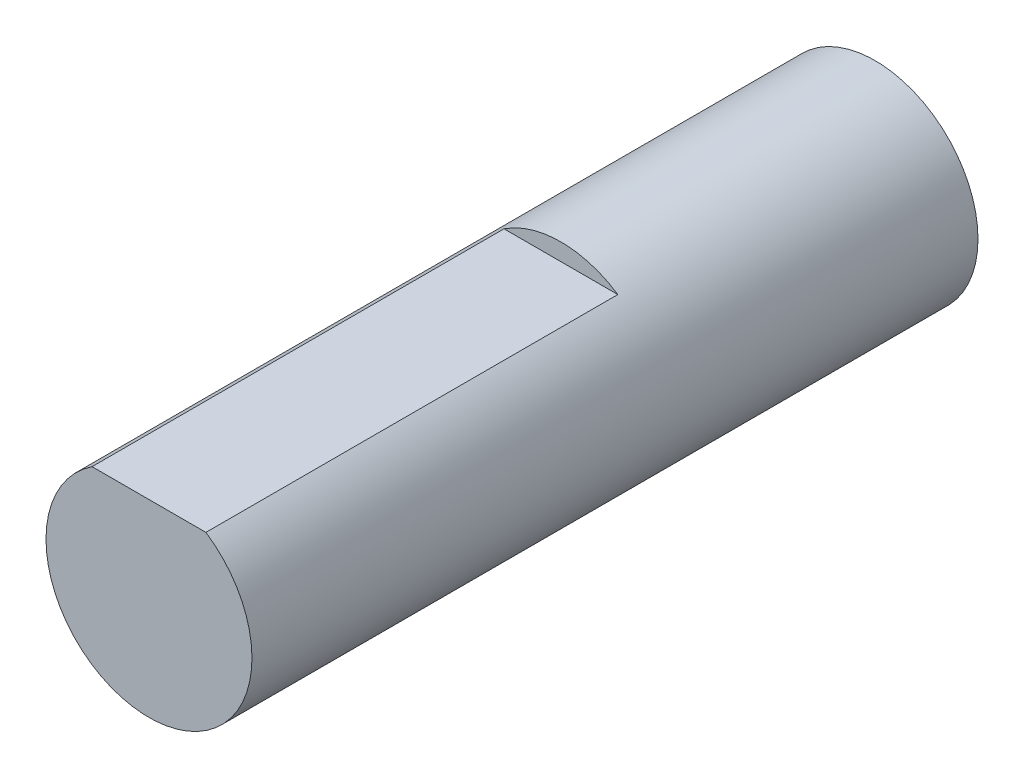
SolidWorks part; units mm, degrees
material "Plain Carbon Steel"
ref_plane "Front Plane" through (0, 0, 0) normal (0, 0, 1) x (1, 0, 0)
ref_plane "Top Plane" through (0, 0, 0) normal (0, 1, 0) x (1, 0, 0)
ref_plane "Right Plane" through (0, 0, 0) normal (1, 0, 0) x (0, 0, -1)
sketch "Sketch1" plane through (0, 0, 0) normal (0, 0, 1) x (1, 0, 0)
  circle A0 centre (0, 0) radius 3
  dimension "D1" = 6
extrude "Boss-Extrude1" add sketch "Sketch1" along normal blind 21.15
sketch "Sketch2" plane through (0, 0, 21.15) normal (0, 0, 1) x (1, 0, 0)
  line L0 (-2.6173, -3) -> (2.2434, -3) construction
  line L1 (-1.6583, 3) -> (1.6583, 3)
  line L2 (-1.6583, 3) -> (-1.6583, 2.5)
  line L3 (-1.6583, 2.5) -> (1.6583, 2.5)
  line L4 (1.6583, 3) -> (1.6583, 2.5)
  circle A0 centre (0, 0) radius 3 construction
  dimension "D1" = 5.5
extrude "Cut-Extrude1" cut sketch "Sketch2" against normal blind 12
